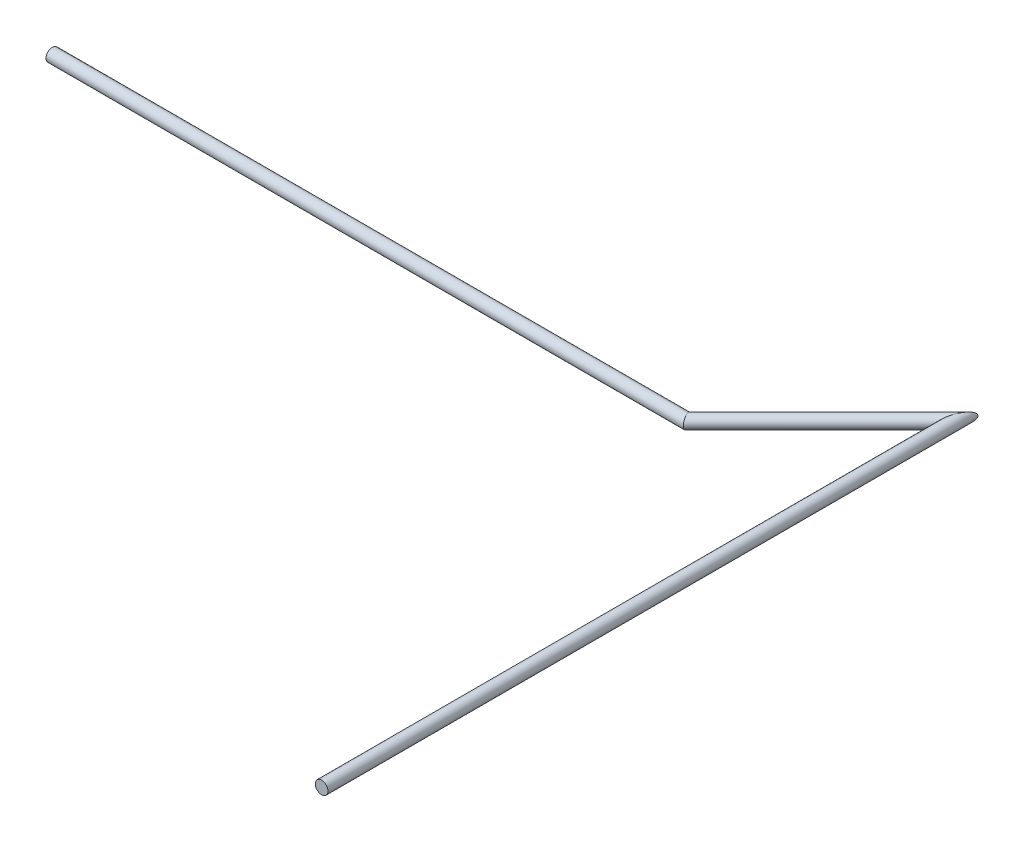
SolidWorks part; units mm, degrees
ref_plane "前视基准面" through (0, 0, 0) normal (0, 0, 1) x (1, 0, 0)
ref_plane "上视基准面" through (0, 0, 0) normal (0, 1, 0) x (1, 0, 0)
ref_plane "右视基准面" through (0, 0, 0) normal (1, 0, 0) x (0, 0, -1)
other "Configuration Table"
sketch3d "3DSketch2"
  line L0 (0, 0, 0) -> (0, 0, 500)
  line L3 (0, 0, 0) -> (-106.066, 0, 106.066)
  line L4 (-106.066, 0, 106.066) -> (-606.066, 0, 106.066)
  dimension "D1" = 150
  dimension "D2" = 500
  dimension "D3" = 45
  dimension "D4" = 500
other "Round-rods ROUND BAR 10(2)"
ref_plane "Plane2" through (0, 0, 0) normal (0, 0, 1) x (1, 0, 0)
sketch "Sketch1" plane through (0, 0, 0) normal (0, 0, 1) x (1, 0, 0)
  circle A0 centre (0, 0) radius 5
  point P2 (0, 0)
  dimension "d" = 10
